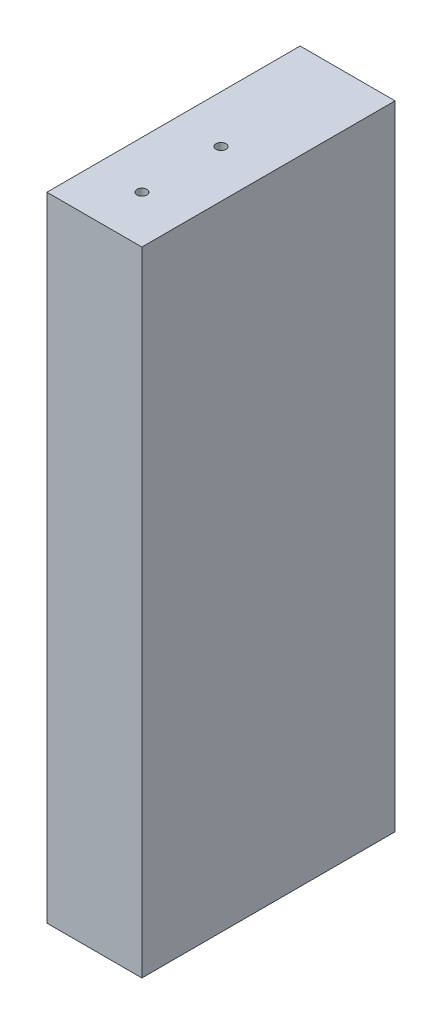
SolidWorks part; units mm, degrees
material "MDF"
ref_plane "Front" through (0, 0, 0) normal (0, 0, 1) x (1, 0, 0)
ref_plane "Top" through (0, 0, 0) normal (0, 1, 0) x (1, 0, 0)
ref_plane "Right" through (0, 0, 0) normal (1, 0, 0) x (0, 0, -1)
sketch "Sketch1" plane through (0, 0, 0) normal (0, 0, 1) x (1, 0, 0)
  line L0 (182.8446, 5942.6348) -> (386.6682, 5942.6348) construction
  line L1 (386.6697, 5942.6348) -> (367.6197, 5942.6348)
  line L2 (386.6697, 5942.6348) -> (386.6697, 6069.6348)
  line L3 (386.6697, 6069.6348) -> (367.6197, 6069.6348)
  line L4 (367.6197, 5942.6348) -> (367.6197, 6069.6348)
  line L5 (391.6372, 6069.6348) -> (189.1946, 6069.6348) construction
  line L6 (386.0251, 5923.5848) -> (422.1231, 6990.3848) construction
  dimension "D1" = 19.05
extrude "Boss-Extrude1" add sketch "Sketch1" along normal blind 50.8
hole_wizard "5/64 (0.07813) Diameter Hole1" positions "Sketch2" profile "Sketch3" hole size "5/64" standard "ANSI Inch"
sketch "Sketch2" plane through (-83.854, -12.3952, -19.0501) normal (0, 0, -1) x (-1, 0, 0)
  point P0 (-481.5892, 6993.255)
  point P9 (-386.3392, 6993.255)
  point P18 (-291.0892, 6993.255)
  point P21 (-295.275, 6965.1359)
  point P33 (-295.275, 6812.7359)
  point P45 (-295.275, 6660.3359)
  point P48 (-285.1664, 6631.4688)
  point P66 (-475.4773, 6631.4688)
  point P69 (-485.0023, 6660.3359)
  point P81 (-485.0023, 6812.7359)
  point P93 (-485.0023, 6965.1359)
  point P96 (-478.3656, 6611.6708)
  point P114 (-287.8656, 6611.6708)
  point P117 (-307.975, 6564.3379)
  point P127 (-307.975, 6488.1379)
  point P130 (-284.9609, 6440.805)
  point P143 (-380.2109, 6440.805)
  point P152 (-475.4609, 6440.805)
  point P155 (-446.8313, 6488.1379)
  point P161 (-446.8313, 6564.3379)
  point P164 (-472.2313, 6396.355)
  point P170 (-472.2313, 6320.155)
  point P173 (-472.6532, 6275.705)
  point P182 (-377.4032, 6275.705)
  point P191 (-282.1532, 6275.705)
  point P194 (-282.575, 6320.155)
  point P200 (-282.575, 6396.355)
  point P203 (-435.5986, 6221.73)
  point P209 (-435.5986, 6145.53)
  point P233 (-450.5925, 6091.555)
  point P242 (-460.9986, 6091.5555)
  point P245 (-460.9986, 6056.63)
  point P251 (-460.9986, 5980.43)
  point P263 (-460.9986, 5945.505)
  point P280 (-282.1532, 5945.505)
  point P284 (-368.6118, 5945.505)
sketch "Sketch3" plane through (397.7353, 6980.8598, -19.0501) normal (1, 0, 0) x (0, 1, 0)
  line L0 (0, 0) -> (0, 38.6962)
  line L1 (0, 38.6962) -> (0.9923, 38.1)
  line L2 (0.9923, 38.1) -> (0.9923, 0)
  line L3 (0.9923, 0) -> (0, 0)
  line L4 (0, 38.6962) -> (-0.9923, 38.1) construction
  line L5 (0, -6.35) -> (0, 107.95) construction
  dimension "Hole Dia." = 1.9845
  dimension "Hole Depth" = 38.1
  dimension "Drill Angle" = 118
hole_wizard "5/64 (0.07813) Diameter Hole2" positions "Sketch4" profile "Sketch5" hole size "5/64" standard "ANSI Inch"
sketch "Sketch4" plane through (94.5697, -12.3952, -19.0501) normal (0, 0, -1) x (-1, 0, 0)
  point P0 (-481.5892, 6993.255)
  point P9 (-386.3392, 6993.255)
  point P18 (-291.0892, 6993.255)
  point P21 (-295.275, 6965.1359)
  point P33 (-295.275, 6812.7359)
  point P45 (-295.275, 6660.3359)
  point P48 (-285.1664, 6631.4688)
  point P66 (-475.4773, 6631.4688)
  point P69 (-485.0023, 6660.3359)
  point P81 (-485.0023, 6812.7359)
  point P93 (-485.0023, 6965.1359)
  point P96 (-478.3656, 6611.6708)
  point P114 (-287.8656, 6611.6708)
  point P117 (-307.975, 6564.3379)
  point P127 (-307.975, 6488.1379)
  point P130 (-284.9609, 6440.805)
  point P143 (-380.2109, 6440.805)
  point P152 (-475.4609, 6440.805)
  point P155 (-446.8313, 6488.1379)
  point P161 (-446.8313, 6564.3379)
  point P164 (-472.2313, 6396.355)
  point P170 (-472.2313, 6320.155)
  point P173 (-472.6532, 6275.705)
  point P182 (-377.4032, 6275.705)
  point P191 (-282.1532, 6275.705)
  point P194 (-282.575, 6320.155)
  point P200 (-282.575, 6396.355)
  point P203 (-435.5986, 6221.73)
  point P209 (-435.5986, 6145.53)
  point P233 (-450.5925, 6091.555)
  point P242 (-460.9986, 6091.5555)
  point P245 (-460.9986, 6056.63)
  point P251 (-460.9986, 5980.43)
  point P263 (-460.9986, 5945.505)
  point P280 (-282.1532, 5945.505)
  point P284 (-368.6118, 5945.505)
sketch "Sketch5" plane through (576.1589, 6980.8598, -19.0501) normal (1, 0, 0) x (0, 1, 0)
  line L0 (0, 0) -> (0, 38.6962)
  line L1 (0, 38.6962) -> (0.9923, 38.1)
  line L2 (0.9923, 38.1) -> (0.9923, 0)
  line L3 (0.9923, 0) -> (0, 0)
  line L4 (0, 38.6962) -> (-0.9923, 38.1) construction
  line L5 (0, -6.35) -> (0, 107.95) construction
  dimension "Hole Dia." = 1.9845
  dimension "Hole Depth" = 38.1
  dimension "Drill Angle" = 118
hole_wizard "5/64 (0.07813) Diameter Hole6" positions "Sketch8" profile "Sketch10" hole size "5/64" standard "ANSI Inch"
sketch "Sketch8" plane through (0, 5942.6348, 0) normal (0, -1, 0) x (-1, 0, 0)
  point P0 (-377.1447, -41.275)
  point P3 (-377.1447, -25.4)
sketch "Sketch10" plane through (377.1447, 5942.6348, 41.275) normal (1, 0, 0) x (0, 0, -1)
  line L0 (0, 0) -> (0, 19.6462)
  line L1 (0, 19.6462) -> (0.9923, 19.05)
  line L2 (0.9923, 19.05) -> (0.9923, 0)
  line L5 (0.9923, 0) -> (0, 0)
  line L10 (0, 19.6462) -> (-0.9923, 19.05) construction
  line L11 (0, -6.35) -> (0, 107.95) construction
  dimension "Hole Dia." = 1.9845
  dimension "Hole Depth" = 19.05
  dimension "Drill Angle" = 118
hole_wizard "5/64 (0.07813) Diameter Hole7" positions "Sketch11" profile "Sketch12" hole size "5/64" standard "ANSI Inch"
sketch "Sketch11" plane through (0, 6069.6348, 0) normal (0, 1, 0) x (1, 0, 0)
  circle A0 centre (377.1447, -41.275) radius 0.9923 construction
  circle A1 centre (377.1447, -25.4) radius 0.9923 construction
  point P0 (377.1447, -41.275)
  point P2 (377.1447, -25.4)
sketch "Sketch12" plane through (377.1447, 6069.6348, 41.275) normal (1, 0, 0) x (0, 0, 1)
  line L0 (0, 0) -> (0, 19.6462)
  line L1 (0, 19.6462) -> (0.9923, 19.05)
  line L2 (0.9923, 19.05) -> (0.9923, 0)
  line L5 (0.9923, 0) -> (0, 0)
  line L10 (0, 19.6462) -> (-0.9923, 19.05) construction
  line L11 (0, -6.35) -> (0, 107.95) construction
  dimension "Hole Dia." = 1.9845
  dimension "Hole Depth" = 19.05
  dimension "Drill Angle" = 118
